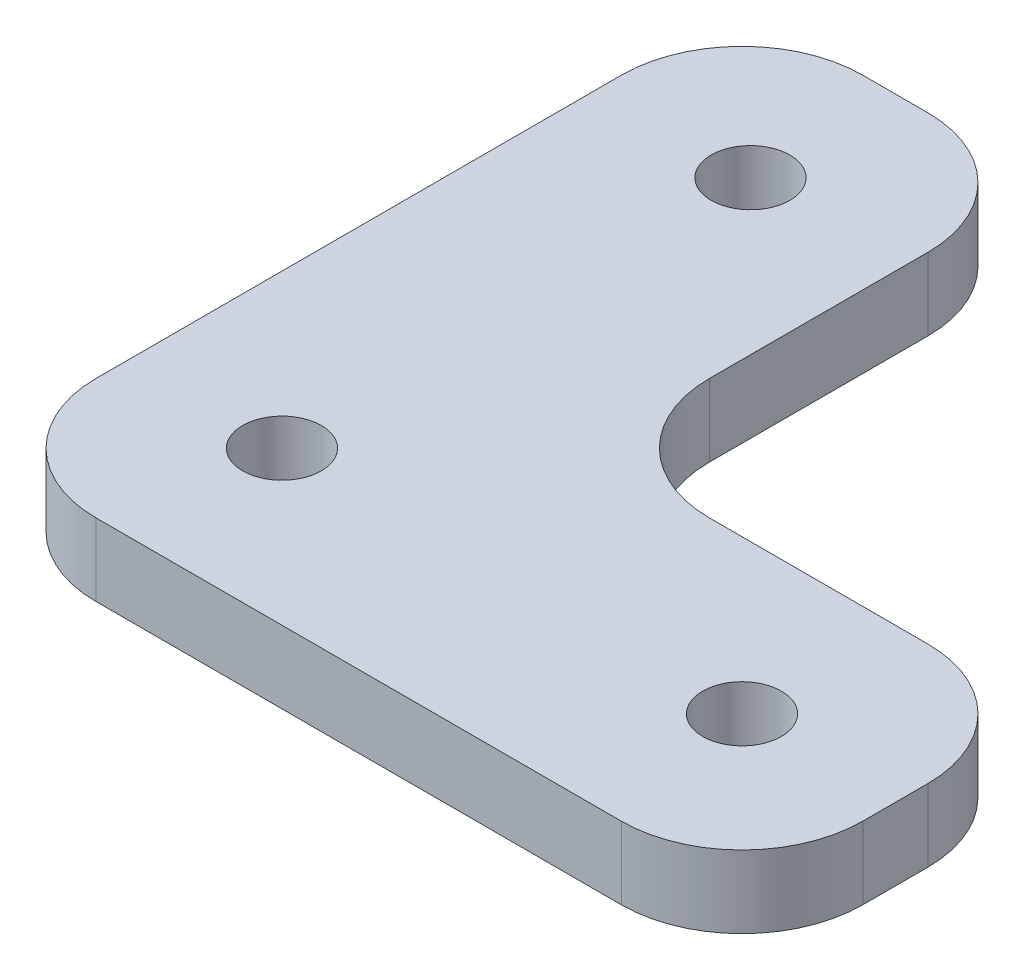
SolidWorks part; units mm, degrees
ref_plane "Front Plane" through (0, 0, 0) normal (0, 0, 1) x (1, 0, 0)
ref_plane "Top Plane" through (0, 0, 0) normal (0, 1, 0) x (1, 0, 0)
ref_plane "Right Plane" through (0, 0, 0) normal (1, 0, 0) x (0, 0, -1)
sketch "Sketch1" plane through (0, 0, 0) normal (0, 1, 0) x (1, 0, 0)
  line L1 (0, 0) -> (25.4, 0)
  line L2 (0, 0) -> (0, 63.5)
  line L3 (0, 63.5) -> (25.4, 63.5)
  line L4 (25.4, 0) -> (25.4, 63.5)
  line L5 (25.4, 0) -> (63.5, 0)
  line L6 (25.4, 0) -> (25.4, 25.4)
  line L7 (25.4, 25.4) -> (63.5, 25.4)
  line L8 (63.5, 0) -> (63.5, 25.4)
  circle A0 centre (50.8, 12.7) radius 3.2576
  circle A1 centre (12.7, 51.5) radius 3.2576
  circle A2 centre (12.7, 12.7) radius 3.2576
  point P12 (12.7, 63.5)
  point P13 (63.5, 12.7)
  point P14 (0, 0)
  point P15 (0, 0)
  point P18 (0, 0)
  dimension "D5" = 6.5151
  dimension "D6" = 6.5151
  dimension "D1" = 25.4
  dimension "D2" = 25.4
  dimension "D3" = 63.5
  dimension "D4" = 63.5
  dimension "D7" = 12
  dimension "D8" = 12.7
extrude "Boss-Extrude1" add sketch "Sketch1" along normal blind 6 contours L1 L4 L3 L2 A2 A1 | L5 L8 L7 L4 A0
fillet "Fillet1" radius 10 6 edges at (63.5, 3, 0) (63.5, 3, -25.4) (25.4, 3, -25.4) (25.4, 3, -63.5) (0, 3, -63.5) (0, 3, 0)
